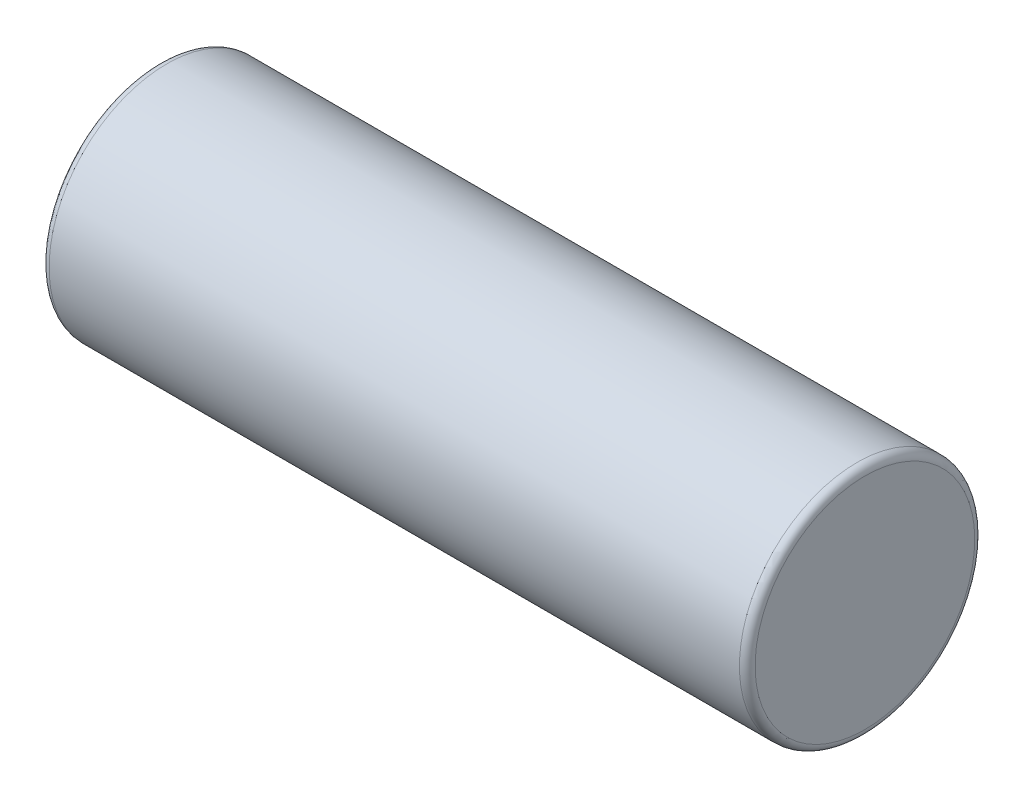
SolidWorks part; units mm, degrees
ref_plane "Front Plane" through (0, 0, 0) normal (0, 0, 1) x (1, 0, 0)
ref_plane "Top Plane" through (0, 0, 0) normal (0, 1, 0) x (1, 0, 0)
ref_plane "Right Plane" through (0, 0, 0) normal (1, 0, 0) x (0, 0, -1)
sketch "Sketch1" plane through (0, 0, 0) normal (1, 0, 0) x (0, 0, -1)
  circle A0 centre (0, 0) radius 3
  dimension "D1" = 6
extrude "Boss-Extrude1" add sketch "Sketch1" along normal mid plane 18
fillet "Fillet1" radius 0.2 2 edges at (-9, 0, -3) (9, 0, -3)
